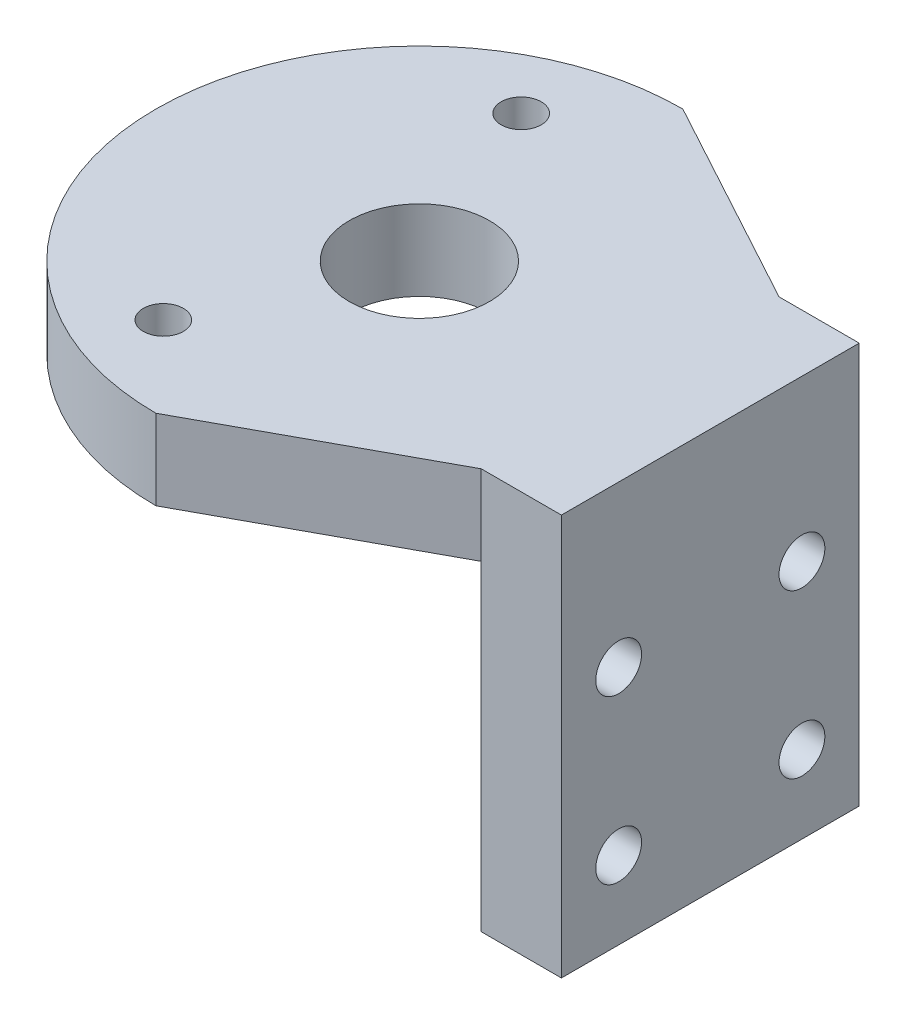
SolidWorks part; units mm, degrees
ref_plane "Front Plane" through (0, 0, 0) normal (0, 0, 1) x (1, 0, 0)
ref_plane "Top Plane" through (0, 0, 0) normal (0, 1, 0) x (1, 0, 0)
ref_plane "Right Plane" through (0, 0, 0) normal (1, 0, 0) x (0, 0, -1)
sketch "Sketch1" plane through (0, 0, 0) normal (0, 1, 0) x (1, 0, 0)
  line L1 (25.4, 23) -> (25.4, -23)
  line L2 (0, 23) -> (25.4, 23)
  line L3 (0, -23) -> (25.4, -23)
  arc A0 (0, 23) -> (0, -23) centre (0, 0) ccw
extrude "Boss-Extrude1" add sketch "Sketch1" against normal blind 7
sketch "Sketch2" plane through (0, -7, 0) normal (0, -1, 0) x (1, 0, 0)
  line L0 (25.4, 23) -> (25.4, -23) construction
  line L1 (25.4, 23) -> (25.4, -23)
  line L2 (18.4, 23) -> (18.4, -23)
  line L3 (18.4, -23) -> (25.4, -23)
  line L4 (18.4, 23) -> (25.4, 23)
  dimension "D1" = 7
extrude "Boss-Extrude2" add sketch "Sketch2" along normal blind 28
sketch "Sketch4" plane through (0, 0, 0) normal (0, 1, 0) x (1, 0, 0)
  circle A0 centre (0, 0) radius 6.125
extrude "Cut-Extrude1" cut sketch "Sketch4" against normal blind 7
sketch "Sketch5" plane through (0, 0, 0) normal (0, 1, 0) x (1, 0, 0)
  line L0 (0, 0) -> (-6.731, 0)
  circle A1 centre (-6.731, 15.621) radius 1.75
  circle A2 centre (-6.731, -15.621) radius 1.75
extrude "Cut-Extrude3" cut sketch "Sketch5" against normal blind 7
sketch "Sketch6" plane through (18.4, 0, 0) normal (-1, 0, 0) x (0, 0, 1)
  line L0 (0, -7) -> (0, -35) construction
  line L2 (13, -7) -> (13, -35)
  line L3 (23, -35) -> (23, -7) construction
  line L4 (13, -35) -> (23, -35)
  line L5 (23, -35) -> (23, -7)
  line L6 (23, -7) -> (13, -7)
  line L7 (-13, -7) -> (-13, -35)
  line L8 (23, -7) -> (-23, -7) construction
  line L9 (23, -35) -> (-23, -35) construction
  line L10 (0, -21) -> (23, -21) construction
  line L11 (0, -21) -> (-23, -21) construction
  line L12 (-23, -35) -> (-23, -7) construction
  line L13 (-11.5, -21) -> (-11.5, -7) construction
  line L14 (-23, -7) -> (23, -7) construction
  line L15 (11.5, -21) -> (11.5, -7) construction
  line L16 (-13, -21) -> (-13, -7) construction
  line L17 (13, -21) -> (13, -7) construction
  line L18 (-13, -35) -> (-23, -35)
  line L19 (-23, -35) -> (-23, -7)
  line L20 (-23, -7) -> (-13, -7)
  dimension "D1" = 1.5
  dimension "D2" = 1.5
extrude "Cut-Extrude4" cut sketch "Sketch6" against normal blind 10
sketch "Sketch7" plane through (0, -7, 0) normal (0, -1, 0) x (1, 0, 0)
  line L0 (0, -23) -> (18.4, -13)
  line L1 (18.4, -13) -> (25.4, -13)
  line L2 (25.4, -13) -> (25.4, -23)
  line L3 (25.4, -23) -> (0, -23)
  line L4 (0, 23) -> (18.4, 13)
  line L5 (18.4, 13) -> (25.4, 13)
  line L6 (25.4, 13) -> (25.4, 23)
  line L7 (25.4, 23) -> (0, 23)
extrude "Cut-Extrude5" cut sketch "Sketch7" against normal blind 10
sketch "Sketch8" plane through (18.4, 0, 0) normal (-1, 0, 0) x (0, 0, 1)
  line L0 (0, -7) -> (0, -35) construction
  line L1 (13, -7) -> (-13, -7) construction
  line L2 (13, -35) -> (-13, -35) construction
  line L3 (-8, -7) -> (-8, -35) construction
  line L4 (8, -7) -> (8, -35) construction
  line L5 (8, -7) -> (-8, -7) construction
  line L6 (8, -14) -> (-8, -14) construction
  line L7 (8, -28.225) -> (-8, -28.225) construction
  circle A0 centre (-8, -14) radius 2
  circle A1 centre (8, -14) radius 2
  circle A2 centre (-8, -28.225) radius 2
  circle A3 centre (8, -28.225) radius 2
  dimension "D1" = 8
  dimension "D2" = 8
  dimension "D3" = 7
  dimension "D4" = 14.225
extrude "Cut-Extrude6" cut sketch "Sketch8" against normal blind 10
